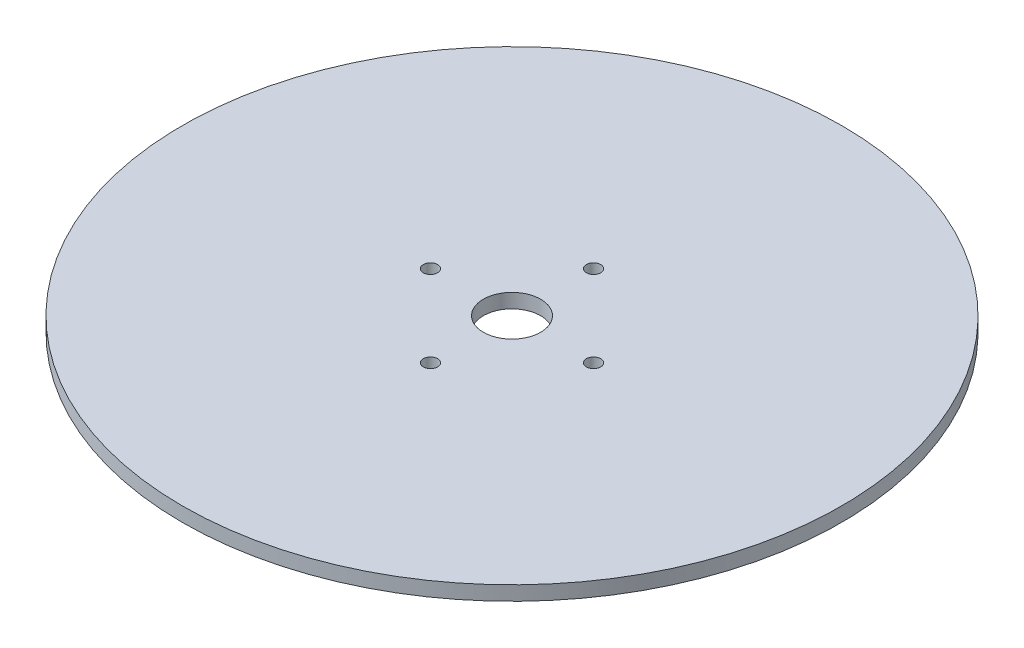
SolidWorks part; units mm, degrees
material "Cedar"
ref_plane "Front Plane" through (0, 0, 0) normal (0, 0, 1) x (1, 0, 0)
ref_plane "Top Plane" through (0, 0, 0) normal (0, 1, 0) x (1, 0, 0)
ref_plane "Right Plane" through (0, 0, 0) normal (1, 0, 0) x (0, 0, -1)
sketch "Sketch1" plane through (0, 0, 0) normal (0, 1, 0) x (1, 0, 0)
  line L0 (0, 21.463) -> (0, 50.8) construction
  line L1 (0, 21.463) -> (0, 0) construction
  circle A0 centre (0, 0) radius 146.05
  circle A1 centre (0, 0) radius 12.7
  circle A6 centre (0, 36.1315) radius 3.175
  circle A7 centre (36.1315, 0) radius 3.175
  circle A8 centre (0, -36.1315) radius 3.175
  circle A9 centre (-36.1315, 0) radius 3.175
  point P8 (0, -0.0226)
  point P15 (0, 0)
  point P17 (0, 0)
  dimension "D1" = 4
extrude "Boss-Extrude1" add sketch "Sketch1" along normal blind 6.35
